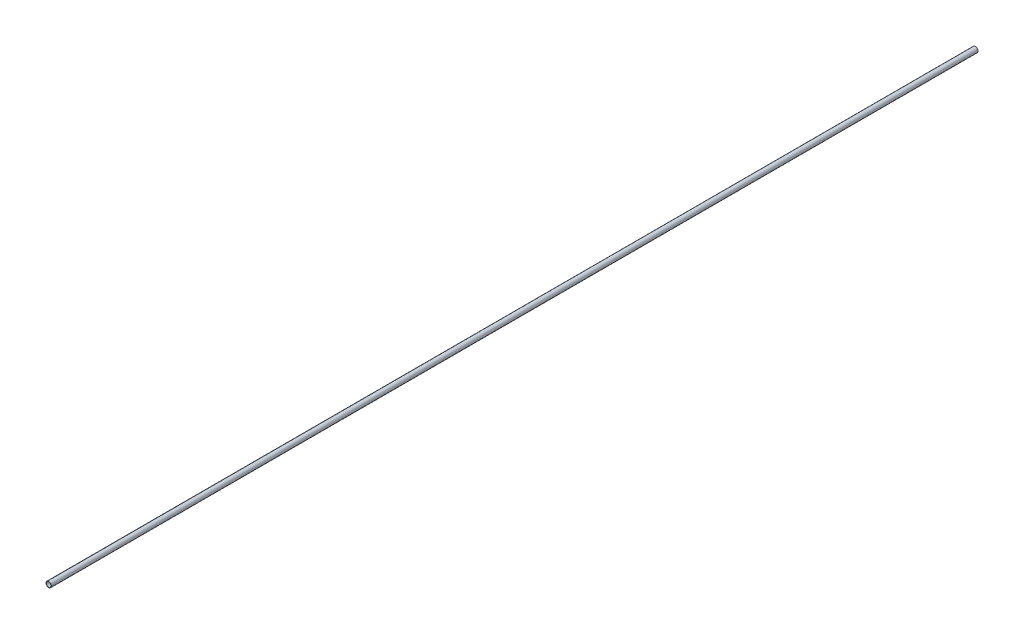
SolidWorks part; units mm, degrees
material "AISI 316 Annealed Stainless Steel Bar (SS)"
ref_plane "Front" through (0, 0, 0) normal (0, 0, 1) x (1, 0, 0)
ref_plane "Top" through (0, 0, 0) normal (0, 1, 0) x (1, 0, 0)
ref_plane "Right" through (0, 0, 0) normal (1, 0, 0) x (0, 0, -1)
sketch "Sketch1" plane through (0, 0, 0) normal (0, 0, 1) x (1, 0, 0)
  circle A0 centre (0, 0) radius 6.35
  circle A1 centre (0, 0) radius 5.5562
  dimension "D1" = 12.7
  dimension "D2" = 0.7937
extrude "Boss-Extrude1" add sketch "Sketch1" along normal blind 2190.75
